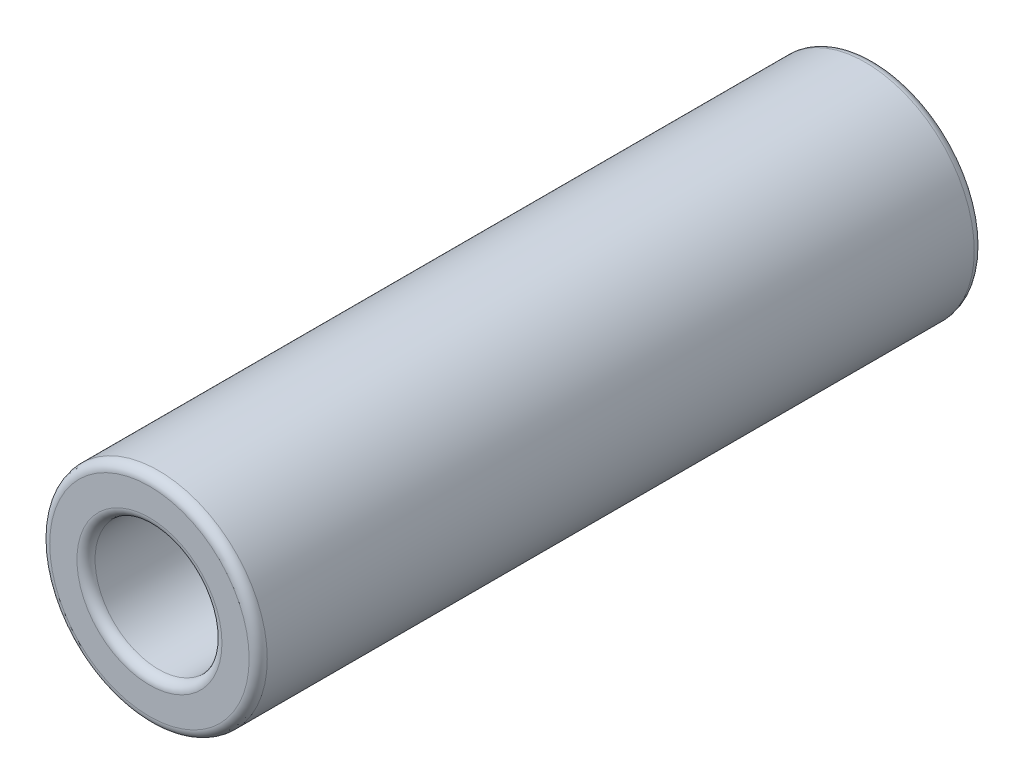
SolidWorks part; units mm, degrees
ref_plane "Płaszczyzna przednia" through (0, 0, 0) normal (0, 0, 1) x (1, 0, 0)
ref_plane "Płaszczyzna górna" through (0, 0, 0) normal (0, 1, 0) x (1, 0, 0)
ref_plane "Płaszczyzna prawa" through (0, 0, 0) normal (1, 0, 0) x (0, 0, -1)
sketch "Szkic1" plane through (0, 0, 0) normal (0, 0, 1) x (1, 0, 0)
  circle A0 centre (0, 0) radius 3.5
  circle A1 centre (0, 0) radius 6
  dimension "D1" = 7
  dimension "D2" = 12
extrude "Dodanie-wyciągnięcie1" add sketch "Szkic1" along normal blind 40
fillet "Zaokrąglenie2" radius 0.5 4 edges at (3.5, 0, 0) (6, 0, 0) (3.5, 0, 40) (6, 0, 40)
